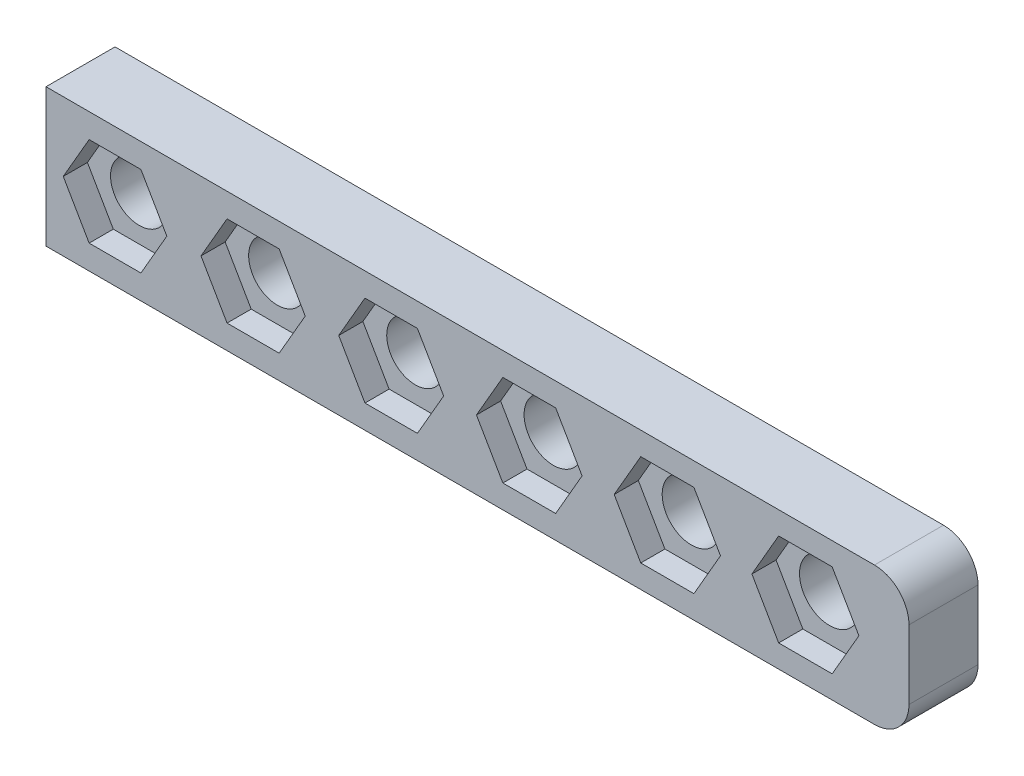
SolidWorks part; units mm, degrees
ref_plane "前视基准面" through (0, 0, 0) normal (0, 0, 1) x (1, 0, 0)
ref_plane "上视基准面" through (0, 0, 0) normal (0, 1, 0) x (1, 0, 0)
ref_plane "右视基准面" through (0, 0, 0) normal (1, 0, 0) x (0, 0, -1)
ref_plane "基准面4" through (0, 0, 0) normal (0, 0, -1) x (-1, 0, 0)
sketch "草图1" plane through (0, 0, 0) normal (0, 0, -1) x (-1, 0, 0)
  line L0 (-125, -106) -> (-125, -126)
  line L1 (-125, -126) -> (0, -126)
  line L2 (0, -126) -> (0, -106)
  line L3 (0, -106) -> (-125, -106)
extrude "凸台-拉伸1" add sketch "草图1" against normal blind 10
sketch "草图2" plane through (0, 0, 10) normal (0, 0, 1) x (1, 0, 0)
  line L0 (93.85, -122.6684) -> (97.7, -116)
  line L1 (97.7, -116) -> (93.85, -109.3316)
  line L2 (93.85, -109.3316) -> (86.15, -109.3316)
  line L3 (86.15, -109.3316) -> (82.3, -116)
  line L4 (82.3, -116) -> (86.15, -122.6684)
  line L5 (86.15, -122.6684) -> (93.85, -122.6684)
extrude "切除-拉伸1" cut sketch "草图2" against normal blind 3.5
sketch "草图3" plane through (0, 0, 10) normal (0, 0, 1) x (1, 0, 0)
  line L0 (73.825, -122.6251) -> (77.65, -116)
  line L1 (77.65, -116) -> (73.825, -109.3749)
  line L2 (73.825, -109.3749) -> (66.175, -109.3749)
  line L3 (66.175, -109.3749) -> (62.35, -116)
  line L4 (62.35, -116) -> (66.175, -122.6251)
  line L5 (66.175, -122.6251) -> (73.825, -122.6251)
extrude "切除-拉伸2" cut sketch "草图3" against normal blind 3.5
sketch "草图4" plane through (0, 0, 10) normal (0, 0, 1) x (1, 0, 0)
  line L0 (53.8, -122.5818) -> (57.6, -116)
  line L1 (57.6, -116) -> (53.8, -109.4182)
  line L2 (53.8, -109.4182) -> (46.2, -109.4182)
  line L3 (46.2, -109.4182) -> (42.4, -116)
  line L4 (42.4, -116) -> (46.2, -122.5818)
  line L5 (46.2, -122.5818) -> (53.8, -122.5818)
extrude "切除-拉伸3" cut sketch "草图4" against normal blind 3.5
sketch "草图5" plane through (0, 0, 10) normal (0, 0, 1) x (1, 0, 0)
  line L0 (33.775, -122.5385) -> (37.55, -116)
  line L1 (37.55, -116) -> (33.775, -109.4615)
  line L2 (33.775, -109.4615) -> (26.225, -109.4615)
  line L3 (26.225, -109.4615) -> (22.45, -116)
  line L4 (22.45, -116) -> (26.225, -122.5385)
  line L5 (26.225, -122.5385) -> (33.775, -122.5385)
extrude "切除-拉伸4" cut sketch "草图5" against normal blind 3.5
sketch "草图6" plane through (0, 0, 10) normal (0, 0, 1) x (1, 0, 0)
  line L0 (13.75, -122.4952) -> (17.5, -116)
  line L1 (17.5, -116) -> (13.75, -109.5048)
  line L2 (13.75, -109.5048) -> (6.25, -109.5048)
  line L3 (6.25, -109.5048) -> (2.5, -116)
  line L4 (2.5, -116) -> (6.25, -122.4952)
  line L5 (6.25, -122.4952) -> (13.75, -122.4952)
extrude "切除-拉伸5" cut sketch "草图6" against normal blind 3.5
sketch "草图7" plane through (0, 0, 10) normal (0, 0, 1) x (1, 0, 0)
  line L0 (113.875, -122.7117) -> (117.75, -116)
  line L1 (117.75, -116) -> (113.875, -109.2883)
  line L2 (113.875, -109.2883) -> (106.125, -109.2883)
  line L3 (106.125, -109.2883) -> (102.25, -116)
  line L4 (102.25, -116) -> (106.125, -122.7117)
  line L5 (106.125, -122.7117) -> (113.875, -122.7117)
extrude "切除-拉伸6" cut sketch "草图7" against normal blind 3.5
hole_wizard "Ø8.7 (8.7) 直径孔1" positions "草图9" profile "草图8" hole size "Ø8.7" standard "ANSI Metric"
sketch "草图9" plane through (0, 0, 0) normal (0, 0, -1) x (-1, 0, 0)
  point P0 (-110, -116)
sketch "草图8" plane through (110, -116, 0) normal (1, 0, 0) x (0, 1, 0)
  line L0 (0, 0) -> (0, 10)
  line L1 (0, 10) -> (4.35, 10)
  line L2 (4.35, 10) -> (4.35, 0)
  line L5 (4.35, 0) -> (0, 0)
  line L11 (0, -6.35) -> (0, 107.95) construction
  dimension "通孔孔直径" = 8.7
  dimension "通孔孔深度" = 10
hole_wizard "Ø8.5 (8.5) 直径孔1" positions "草图11" profile "草图10" hole size "Ø8.5" standard "ANSI Metric"
sketch "草图11" plane through (0, 0, 0) normal (0, 0, -1) x (-1, 0, 0)
  point P0 (-70, -116)
  point P1 (-90, -116)
sketch "草图10" plane through (70, -116, 0) normal (1, 0, 0) x (0, 1, 0)
  line L0 (0, 0) -> (0, 10)
  line L1 (0, 10) -> (4.25, 10)
  line L2 (4.25, 10) -> (4.25, 0)
  line L5 (4.25, 0) -> (0, 0)
  line L11 (0, -6.35) -> (0, 107.95) construction
  dimension "通孔孔直径" = 8.5
  dimension "通孔孔深度" = 10
hole_wizard "Ø8.3 (8.3) 直径孔1" positions "草图13" profile "草图12" hole size "Ø8.3" standard "ANSI Metric"
sketch "草图13" plane through (0, 0, 0) normal (0, 0, -1) x (-1, 0, 0)
  point P0 (-30, -116)
  point P1 (-50, -116)
  point P2 (-10, -116)
sketch "草图12" plane through (30, -116, 0) normal (1, 0, 0) x (0, 1, 0)
  line L0 (0, 0) -> (0, 10)
  line L1 (0, 10) -> (4.15, 10)
  line L2 (4.15, 10) -> (4.15, 0)
  line L5 (4.15, 0) -> (0, 0)
  line L11 (0, -6.35) -> (0, 107.95) construction
  dimension "通孔孔直径" = 8.3
  dimension "通孔孔深度" = 10
fillet "圆角1" radius 5 2 edges at (125, -106, 5) (125, -126, 5)
